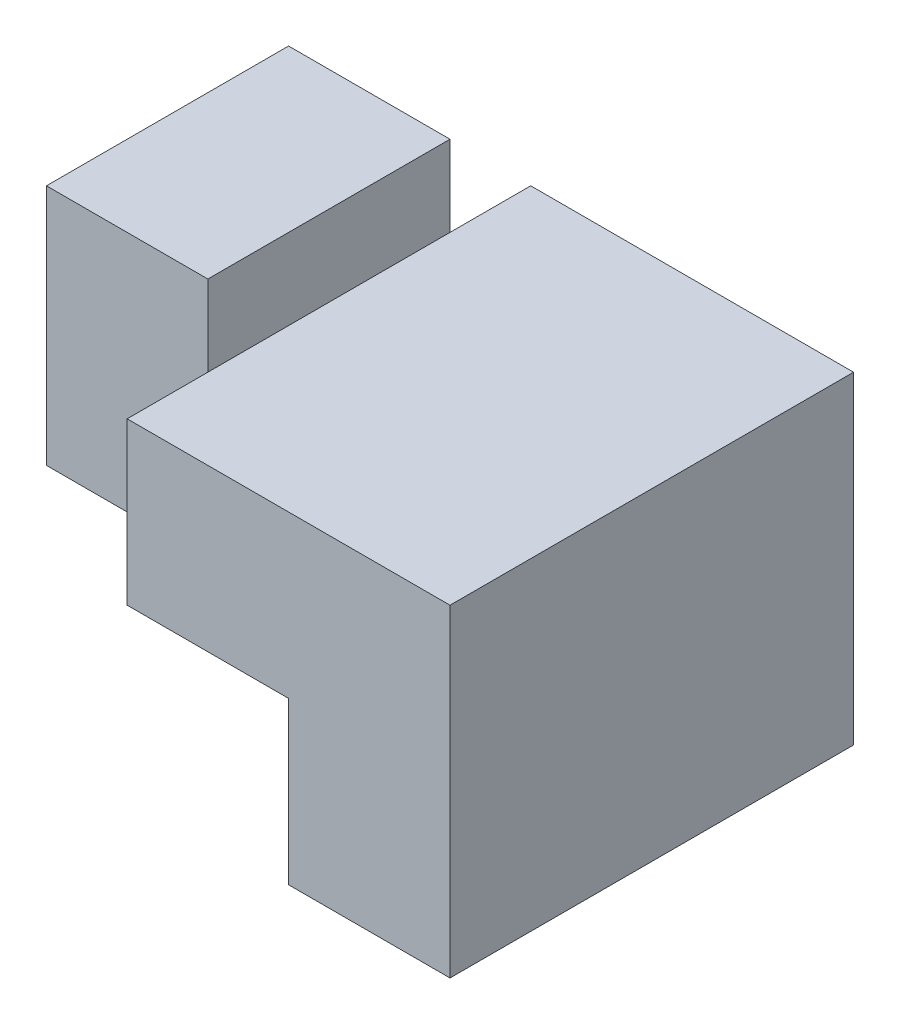
SolidWorks part; units mm, degrees
ref_plane "Front Plane" through (0, 0, 0) normal (0, 0, 1) x (1, 0, 0)
ref_plane "Top Plane" through (0, 0, 0) normal (0, 1, 0) x (1, 0, 0)
ref_plane "Right Plane" through (0, 0, 0) normal (1, 0, 0) x (0, 0, -1)
sketch "Sketch1" plane through (0, 0, 0) normal (0, 0, 1) x (1, 0, 0)
  line L1 (0, 0) -> (30, 0)
  line L2 (0, 0) -> (0, 25)
  line L3 (0, 25) -> (30, 25)
  line L4 (30, 0) -> (30, 25)
  dimension "D1" = 25
  dimension "D2" = 30
extrude "Boss-Extrude1" add sketch "Sketch1" along normal blind 25
sketch "Sketch2" plane through (0, 0, 25) normal (0, 0, 1) x (1, 0, 0)
  line L1 (0, 0) -> (10, 0)
  line L2 (0, 0) -> (0, 10)
  line L3 (0, 10) -> (10, 10)
  line L4 (10, 0) -> (10, 10)
  dimension "D1" = 10
  dimension "D2" = 10
extrude "Cut-Extrude3" cut sketch "Sketch2" against normal blind 10
sketch "Sketch4" plane through (0, 0, 25) normal (0, 0, 1) x (1, 0, 0)
  line L1 (10, 0) -> (20, 0)
  line L2 (10, 0) -> (10, 5)
  line L3 (10, 5) -> (20, 5)
  line L4 (20, 0) -> (20, 5)
  dimension "D1" = 10
  dimension "D2" = 5
extrude "Cut-Extrude4" cut sketch "Sketch4" against normal blind 25
sketch "Sketch5" plane through (0, 0, 0) normal (0, 0, -1) x (-1, 0, 0)
  line L1 (-10, 0) -> (0, 0)
  line L2 (-10, 0) -> (-10, 10)
  line L3 (-10, 10) -> (0, 10)
  line L4 (0, 0) -> (0, 10)
extrude "Cut-Extrude5" cut sketch "Sketch5" against normal blind 10
sketch "Sketch6" plane through (0, 0, 25) normal (0, 0, 1) x (1, 0, 0)
  line L1 (30, 25) -> (10, 25)
  line L2 (30, 25) -> (30, 20)
  line L3 (30, 20) -> (10, 20)
  line L4 (10, 25) -> (10, 20)
  dimension "D1" = 5
  dimension "D2" = 20
extrude "Cut-Extrude6" cut sketch "Sketch6" against normal blind 25
sketch "Sketch7" plane through (0, 25, 0) normal (0, 1, 0) x (1, 0, 0)
  line L0 (10, 0) -> (10, -25) construction
  line L1 (0, 0) -> (10, 0)
  line L2 (0, 0) -> (0, -5)
  line L3 (0, -5) -> (10, -5)
  line L4 (10, 0) -> (10, -5)
  line L6 (0, -25) -> (10, -25)
  line L7 (0, -25) -> (0, -20)
  line L8 (0, -20) -> (10, -20)
  line L9 (10, -25) -> (10, -20)
  dimension "D1" = 5
  dimension "D2" = 5
extrude "Cut-Extrude7" cut sketch "Sketch7" against normal blind 25
sketch "Sketch8" plane through (0, 0, 25) normal (0, 0, 1) x (1, 0, 0)
  line L1 (10, 5) -> (20, 5)
  line L2 (10, 5) -> (10, 10)
  line L3 (10, 10) -> (20, 10)
  line L4 (20, 5) -> (20, 10)
  dimension "D1" = 10
  dimension "D2" = 5
extrude "Cut-Extrude8" cut sketch "Sketch8" against normal blind 5
sketch "Sketch9" plane through (0, 0, 0) normal (0, 0, -1) x (-1, 0, 0)
  line L1 (-20, 5) -> (-10, 5)
  line L2 (-20, 5) -> (-20, 10)
  line L3 (-20, 10) -> (-10, 10)
  line L4 (-10, 5) -> (-10, 10)
extrude "Cut-Extrude9" cut sketch "Sketch9" against normal blind 5
